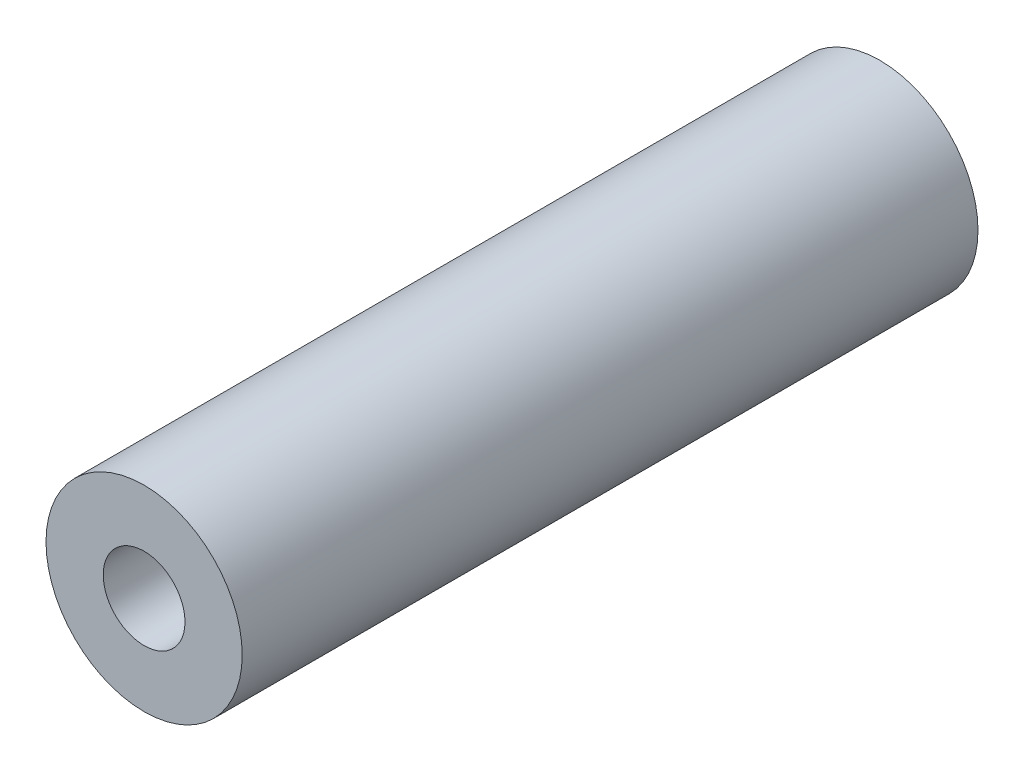
SolidWorks part; units mm, degrees
material "Brass"
ref_plane "Front Plane" through (0, 0, 0) normal (0, 0, 1) x (1, 0, 0)
ref_plane "Top Plane" through (0, 0, 0) normal (0, 1, 0) x (1, 0, 0)
ref_plane "Right Plane" through (0, 0, 0) normal (1, 0, 0) x (0, 0, -1)
sketch "Sketch1" plane through (0, 0, 0) normal (0, 0, 1) x (1, 0, 0)
  circle A0 centre (0, 0) radius 6
  dimension "D1" = 12
extrude "Boss-Extrude1" add sketch "Sketch1" along normal blind 45
sketch "Sketch2" plane through (0, 0, 45) normal (0, 0, 1) x (1, 0, 0)
  circle A0 centre (0, 0) radius 2.1
  point P0 (0, 0)
  dimension "D1" = 4.2
extrude "Cut-Extrude1" cut sketch "Sketch2" against normal through all
sketch "Sketch5" plane through (0, 0, 45) normal (0, 0, 1) x (1, 0, 0)
  circle A0 centre (0, 0) radius 2.5
  dimension "D1" = 5
extrude "Cut-Extrude2" cut sketch "Sketch5" along direction (0, 0, 1) on the side against the normal mid plane 45
